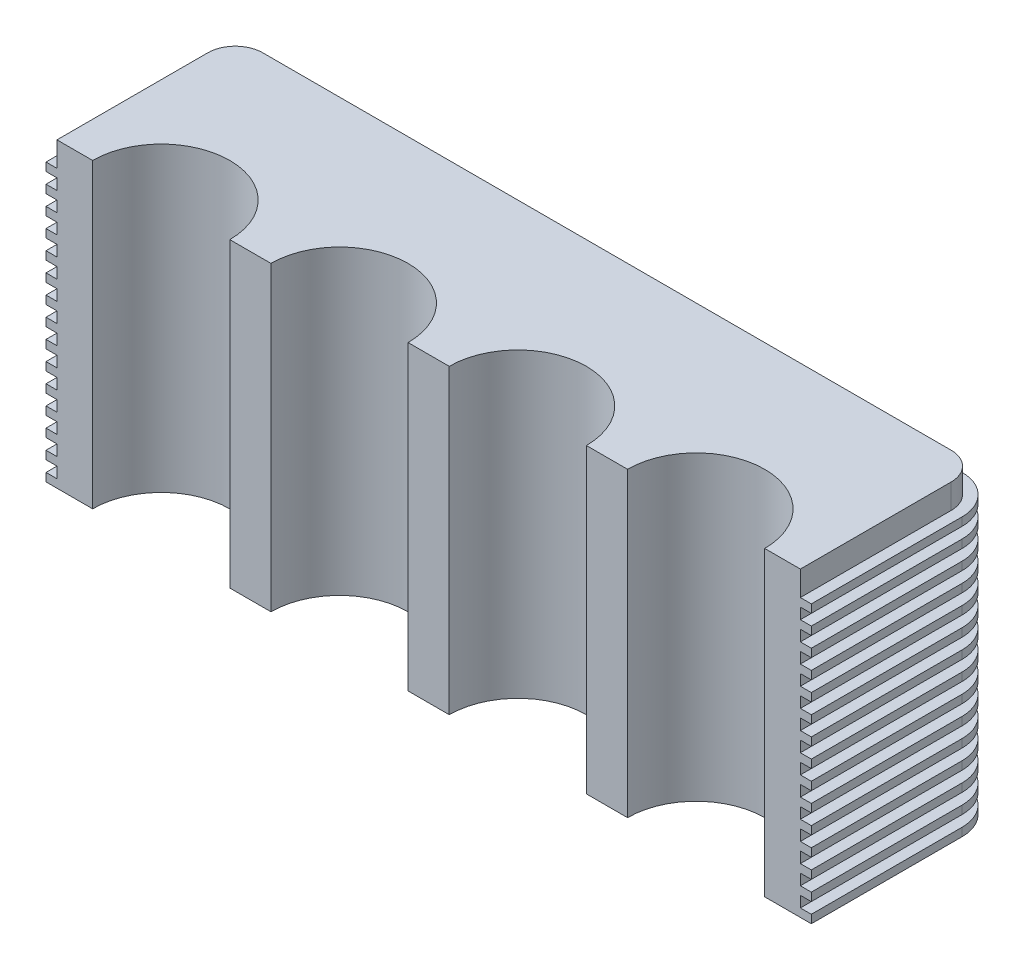
SolidWorks part; units mm, degrees
ref_plane "Front Plane" through (0, 0, 0) normal (0, 0, 1) x (1, 0, 0)
ref_plane "Top Plane" through (0, 0, 0) normal (0, 1, 0) x (1, 0, 0)
ref_plane "Right Plane" through (0, 0, 0) normal (1, 0, 0) x (0, 0, -1)
sketch "Sketch1" plane through (0, 0, 0) normal (0, 1, 0) x (1, 0, 0)
  line L0 (135.5, 0) -> (135.5, 65) construction
  line L1 (0, 0) -> (13, 0)
  line L2 (0, 0) -> (0, 55)
  line L3 (10, 65) -> (261, 65)
  line L4 (271, 0) -> (271, 55)
  line L5 (63, 0) -> (78, 0)
  line L6 (258, 0) -> (271, 0)
  line L7 (193, 0) -> (208, 0)
  line L8 (128, 0) -> (143, 0)
  arc A0 (271, 55) -> (261, 65) centre (261, 55) ccw
  arc A1 (10, 65) -> (0, 55) centre (10, 55) ccw
  arc A2 (208, 0) -> (258, 0) centre (233, 0) cw
  arc A3 (143, 0) -> (193, 0) centre (168, 0) cw
  arc A4 (63, 0) -> (13, 0) centre (38, 0) ccw
  arc A5 (128, 0) -> (78, 0) centre (103, 0) ccw
  dimension "D1" = 10
  dimension "D4" = 25
  dimension "D6" = 25
  dimension "D2" = 271
  dimension "D3" = 65
  dimension "D5" = 13
  dimension "D7" = 15
extrude "Boss-Extrude1" add sketch "Sketch1" along normal blind 110
sketch "Sketch2" plane through (0, 0, 0) normal (0, 1, 0) x (1, 0, 0)
  line L0 (275, 0) -> (275, 55)
  line L1 (261, 69) -> (10, 69)
  line L2 (-4, 55) -> (-4, 0)
  line L3 (271, 0) -> (275, 0)
  line L4 (0, 0) -> (-4, 0)
  line L8 (0, 0) -> (13, 0)
  line L9 (0, 55) -> (0, 0)
  line L10 (261, 65) -> (10, 65)
  line L11 (271, 0) -> (271, 55)
  line L12 (258, 0) -> (271, 0)
  line L13 (193, 0) -> (208, 0)
  line L14 (128, 0) -> (143, 0)
  line L15 (63, 0) -> (78, 0)
  line L17 (0, 55) -> (0, 0)
  line L18 (261, 65) -> (10, 65)
  line L19 (271, 0) -> (271, 55)
  arc A0 (275, 55) -> (261, 69) centre (261, 55) ccw
  arc A1 (10, 69) -> (-4, 55) centre (10, 55) ccw
  arc A6 (10, 65) -> (0, 55) centre (10, 55) ccw
  arc A7 (271, 55) -> (261, 65) centre (261, 55) ccw
  arc A8 (258, 0) -> (208, 0) centre (233, 0) ccw
  arc A9 (193, 0) -> (143, 0) centre (168, 0) ccw
  arc A10 (128, 0) -> (78, 0) centre (103, 0) ccw
  arc A11 (63, 0) -> (13, 0) centre (38, 0) ccw
  arc A12 (10, 65) -> (0, 55) centre (10, 55) ccw
  arc A13 (271, 55) -> (261, 65) centre (261, 55) ccw
  dimension "D1" = 0
  dimension "D2" = 4
extrude "Boss-Extrude2" add sketch "Sketch2" along normal blind 3 contours L1 A1 L2 L4 L17 A12 L18 A13 L19 L3 L0 A0
pattern_linear "LPattern1" count 15 spacing 7 along (0, 1, 0) of "Boss-Extrude2"
